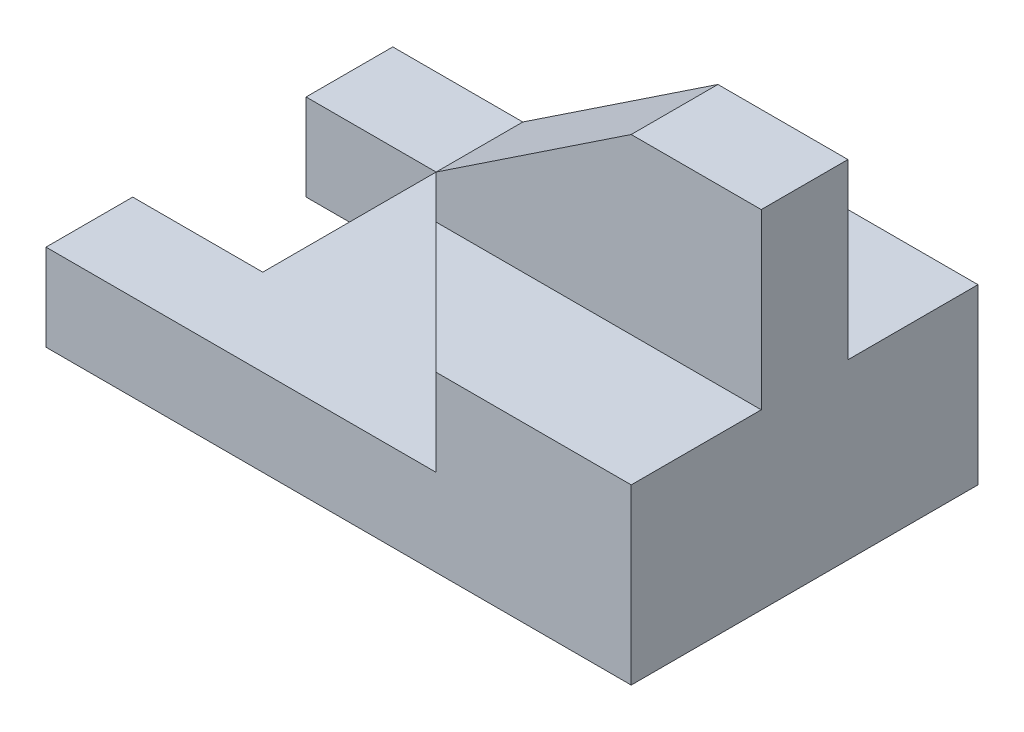
SolidWorks part; units mm, degrees
ref_plane "Front" through (0, 0, 0) normal (0, 0, 1) x (1, 0, 0)
ref_plane "Top" through (0, 0, 0) normal (0, 1, 0) x (1, 0, 0)
ref_plane "Right" through (0, 0, 0) normal (1, 0, 0) x (0, 0, -1)
sketch "Sketch2" plane through (0, 0, 0) normal (0, 1, 0) x (1, 0, 0)
  line L1 (-6.75, -4) -> (6.75, -4)
  line L2 (-6.75, -4) -> (-6.75, 4)
  line L3 (-6.75, 4) -> (6.75, 4)
  line L4 (6.75, -4) -> (6.75, 4)
  line L5 (-6.75, -4) -> (6.75, 4) construction
  line L6 (-6.75, 4) -> (6.75, -4) construction
  line L7 (-6.75, 2) -> (-3.75, 2)
  line L8 (-6.75, 2) -> (-6.75, -2)
  line L9 (-6.75, -2) -> (-3.75, -2)
  line L10 (-3.75, 2) -> (-3.75, -2)
  point P0 (0, 0)
  dimension "D1" = 8
  dimension "D2" = 13.5
  dimension "D3" = 3
  dimension "D4" = 4
  dimension "D5" = 2
extrude "Boss-Extrude1" add sketch "Sketch2" along normal blind 2 contours L7 L10 L9 L2 L1 L4 L3
sketch "Sketch3" plane through (0, 2, 0) normal (0, 1, 0) x (1, 0, 0)
  line L0 (6.75, 4) -> (2.25, 4)
  line L1 (-6.75, 4) -> (6.75, 4) construction
  line L2 (2.25, 4) -> (-0.75, 1)
  line L3 (-0.75, 1) -> (-0.75, -1)
  line L4 (-0.75, -1) -> (2.25, -4)
  line L5 (-6.75, -4) -> (6.75, -4) construction
  line L6 (2.25, -4) -> (6.75, -4)
  line L7 (6.75, -4) -> (6.75, 4)
  dimension "D1" = 4.5
  dimension "D2" = 4.5
  dimension "D3" = 2
  dimension "D4" = 3
  dimension "D5" = 3
extrude "Boss-Extrude2" add sketch "Sketch3" along normal blind 2
sketch "Sketch5" plane through (0, 0, 0) normal (0, 0, 1) x (1, 0, 0)
  line L1 (3.75, 8) -> (6.75, 8)
  line L2 (6.75, 8) -> (6.75, 4)
  line L3 (6.75, 4) -> (-0.75, 4)
  line L4 (-0.75, 4) -> (-0.75, 5)
  line L5 (-0.75, 5) -> (3.75, 8)
  dimension "D1" = 3
  dimension "D2" = 1
  dimension "D3" = 3
extrude "Boss-Extrude3" add sketch "Sketch5" along normal mid plane 2
